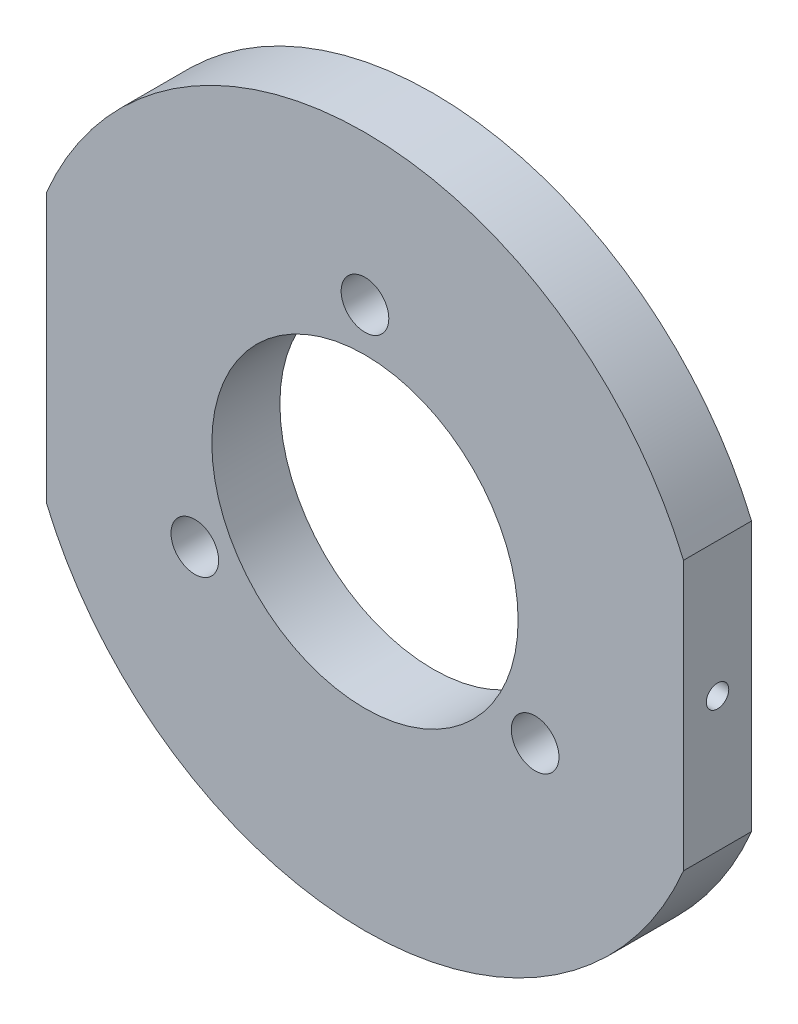
SolidWorks part; units mm, degrees
ref_plane "Front Plane" through (0, 0, 0) normal (0, 0, 1) x (1, 0, 0)
ref_plane "Top Plane" through (0, 0, 0) normal (0, 1, 0) x (1, 0, 0)
ref_plane "Right Plane" through (0, 0, 0) normal (1, 0, 0) x (0, 0, -1)
sketch "Sketch1" plane through (0, 0, 0) normal (0, 0, 1) x (1, 0, 0)
  line L1 (-46.8, 19.7585) -> (-46.8, -19.7585)
  line L2 (0, 0) -> (0, 50.8) construction
  line L3 (46.8, 19.7585) -> (46.8, -19.7585)
  arc A0 (-46.8, -19.7585) -> (46.8, -19.7585) centre (0, 0) ccw
  circle A1 centre (0, 0) radius 22.5
  circle A3 centre (0, 28.8675) radius 3.5
  circle A6 centre (25, -14.4338) radius 3.5
  circle A7 centre (-25, -14.4338) radius 3.5
  arc A8 (46.8, 19.7585) -> (-46.8, 19.7585) centre (0, 0) ccw
  point P13 (0, 0)
  point P14 (0, 0)
  dimension "D1" = 101.6
  dimension "D2" = 45
  dimension "D4" = 7
  dimension "D6" = 4
  dimension "D3" = 50
  dimension "D5" = 3
extrude "Boss-Extrude1" add sketch "Sketch1" along normal blind 10 contours L3 A8 L1 A0 A1 A3 A6 A7
sketch "Sketch2" plane through (46.8, 0, 0) normal (1, 0, 0) x (0, 0, -1)
  line L0 (-10, 0) -> (0, 0) construction
  line L1 (-10, 19.7585) -> (-10, -19.7585) construction
  point P5 (-5, 0)
hole_wizard "M4x0.7 Tapped Hole1" positions "3DSketch1" profile "Sketch4" tap size "M4x0.7" standard "ANSI Metric"
sketch3d "3DSketch1"
  point P0 (46.8, 0, 5)
sketch "Sketch4" plane through (46.8, 0, 5) normal (0, 1, 0) x (0, 0, -1)
  line L0 (0, 0) -> (0, 15.9914)
  line L1 (0, 15.9914) -> (1.65, 15)
  line L2 (1.65, 15) -> (1.65, 0)
  line L5 (1.65, 0) -> (0, 0)
  line L10 (0, 15.9914) -> (-1.65, 15) construction
  line L11 (0, -6.35) -> (0, 107.95) construction
  dimension "Tap Drill Dia." = 3.3
  dimension "Tap Drill Depth" = 15
  dimension "Drill Angle" = 118
cosmetic thread "Hole Thread1" parameters "D1"=8, "D2"=4
mirror "Mirror1" about plane through (0, 0, 0) normal (1, 0, 0) of "M4x0.7 Tapped Hole1"
cosmetic thread "Hole Thread2" parameters "D1"=8, "D2"=4
